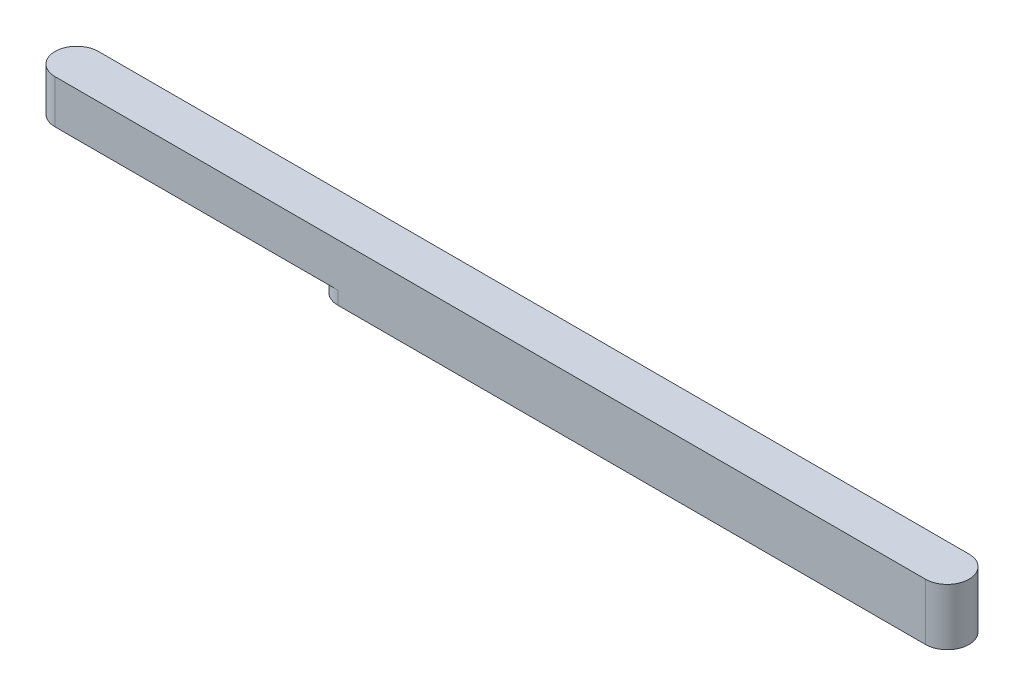
SolidWorks part; units mm, degrees
ref_plane "정면" through (0, 0, 0) normal (0, 0, 1) x (1, 0, 0)
ref_plane "윗면" through (0, 0, 0) normal (0, 1, 0) x (1, 0, 0)
ref_plane "우측면" through (0, 0, 0) normal (1, 0, 0) x (0, 0, -1)
sketch "스케치1" plane through (0, 0, 0) normal (0, 1, 0) x (1, 0, 0)
  line L0 (-156.724, 0) -> (140.546, 0) construction
  line L1 (0, 97.7755) -> (0, -119.818) construction
  line L2 (-100, 0) -> (100, 0) construction
  line L3 (-100, 5) -> (100, 5)
  line L4 (-100, -5) -> (100, -5)
  arc A0 (-100, 5) -> (-100, -5) centre (-100, 0) ccw
  arc A1 (100, -5) -> (100, 5) centre (100, 0) ccw
  point P7 (0, 0)
  dimension "D1" = 200
  dimension "D2" = 10
extrude "보스-돌출1" add sketch "스케치1" along normal mid plane 10
sketch "스케치3" plane through (0, -5, 0) normal (0, -1, 0) x (1, 0, 0)
  line L4 (-73.687, -2.595) -> (-62.1341, -1.9)
  line L5 (-62.1341, 1.9) -> (-73.687, 2.595)
  line L6 (-78.173, 2.595) -> (-89.7259, 1.9)
  line L7 (-89.7259, -1.9) -> (-78.173, -2.595)
  circle A6 centre (-75.93, 0) radius 2.345
  arc A7 (-73.687, -2.595) -> (-73.687, 2.595) centre (-75.93, 0) ccw
  arc A8 (-62.1341, -1.9) -> (-62.1341, 1.9) centre (-62.2484, 0) ccw
  circle A9 centre (-75.93, 0) radius 3.43
  arc A10 (-78.173, 2.595) -> (-78.173, -2.595) centre (-75.93, 0) ccw
  arc A11 (-89.7259, 1.9) -> (-89.7259, -1.9) centre (-89.6116, 0) ccw
  circle A13 centre (-61.86, 0) radius 0.515
  circle A14 centre (-63.824, 0) radius 1
  circle A15 centre (-65.788, 0) radius 0.515
  circle A16 centre (-67.752, 0) radius 1
  circle A17 centre (-69.716, 0) radius 0.515
  circle A18 centre (-71.68, 0) radius 0.515
  circle A19 centre (-90, 0) radius 0.515
  circle A20 centre (-88.036, 0) radius 1
  circle A21 centre (-86.072, 0) radius 0.515
  circle A22 centre (-84.108, 0) radius 1
  circle A23 centre (-80.18, 0) radius 0.515
  circle A24 centre (-82.144, 0) radius 0.515
  point P13 (-100, 0)
  point P39 (-90, 0)
  dimension "D2" = 2
  dimension "D3" = 2
  dimension "D4" = 2
  dimension "D5" = 2
  dimension "D6" = 1.03
  dimension "D1" = 10
extrude "컷-돌출1" cut sketch "스케치3" against normal blind 6 contours A19 | A20 | A21 | A22 | A24 | A23 | A6 | A18 | A17 | A16 | A15 | A13 | A14
sketch "스케치5" plane through (0, -5, 0) normal (0, -1, 0) x (1, 0, 0)
  line L0 (100, 0) -> (-35, 0) construction
  line L1 (100, -5) -> (-35, -5)
  line L2 (100, 5) -> (-35, 5)
  arc A0 (100, -5) -> (100, 5) centre (100, 0) ccw
  arc A1 (-35, 5) -> (-35, -5) centre (-35, 0) ccw
  arc A2 (100, -5) -> (100, 5) centre (100, 0) ccw construction
  point P4 (32.5, 0)
  dimension "D1" = 135
extrude "보스-돌출2" add sketch "스케치5" along normal blind 3
sketch "스케치6" plane through (0, -8, 0) normal (0, -1, 0) x (1, 0, 0)
  line L0 (-35, 0) -> (100, 0) construction
  line L1 (-35, 3) -> (100, 3)
  line L2 (-35, -3) -> (100, -3)
  line L3 (100, 5) -> (-35, 5) construction
  arc A0 (-35, 3) -> (-35, -3) centre (-35, 0) ccw
  arc A1 (100, -3) -> (100, 3) centre (100, 0) ccw
  point P4 (32.5, 0)
  dimension "D1" = 2
extrude "컷-돌출2" cut sketch "스케치6" against normal blind 10
